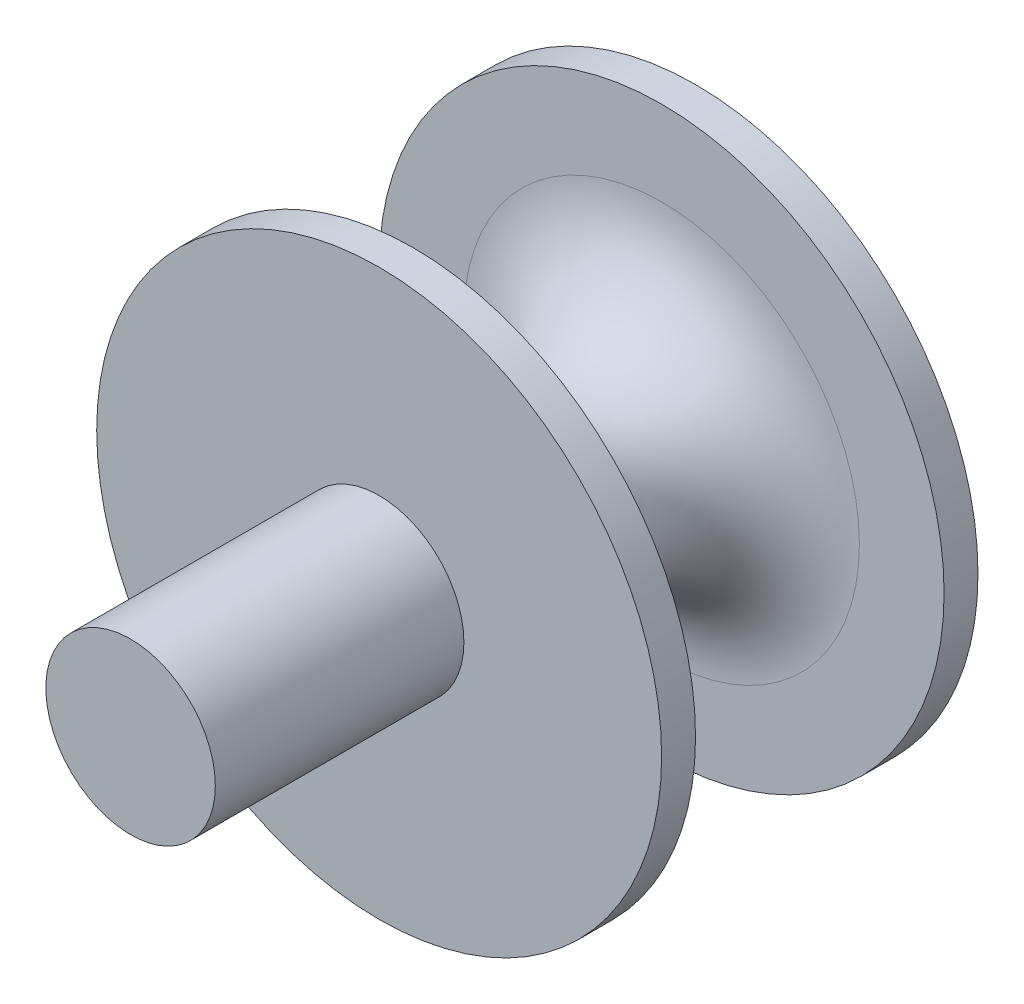
SolidWorks part; units mm, degrees
ref_plane "Alzado" through (0, 0, 0) normal (0, 0, 1) x (1, 0, 0)
ref_plane "Planta" through (0, 0, 0) normal (0, 1, 0) x (1, 0, 0)
ref_plane "Vista lateral" through (0, 0, 0) normal (1, 0, 0) x (0, 0, -1)
sketch "Croquis1" plane through (0, 0, 0) normal (0, 0, 1) x (1, 0, 0)
  circle A0 centre (0, 0) radius 7.5
  dimension "D1" = 15
extrude "Saliente-Extruir2" add sketch "Croquis1" along normal blind 50
sketch "Croquis4" plane through (0, 0, 0) normal (0, 0, 1) x (1, 0, 0)
  circle A0 centre (0, 0) radius 25
  dimension "D1" = 50
extrude "Saliente-Extruir3" add sketch "Croquis4" along normal blind 3
sketch "Croquis5" plane through (0, 0, 0) normal (0, 0, 1) x (1, 0, 0)
  circle A0 centre (0, 0) radius 25
extrude "Saliente-Extruir4" add sketch "Croquis5" along normal blind 3 from offset 25
fillet "Redondeo2" radius 10 2 edges at (7.5, 0, 3) (7.5, 0, 25)
